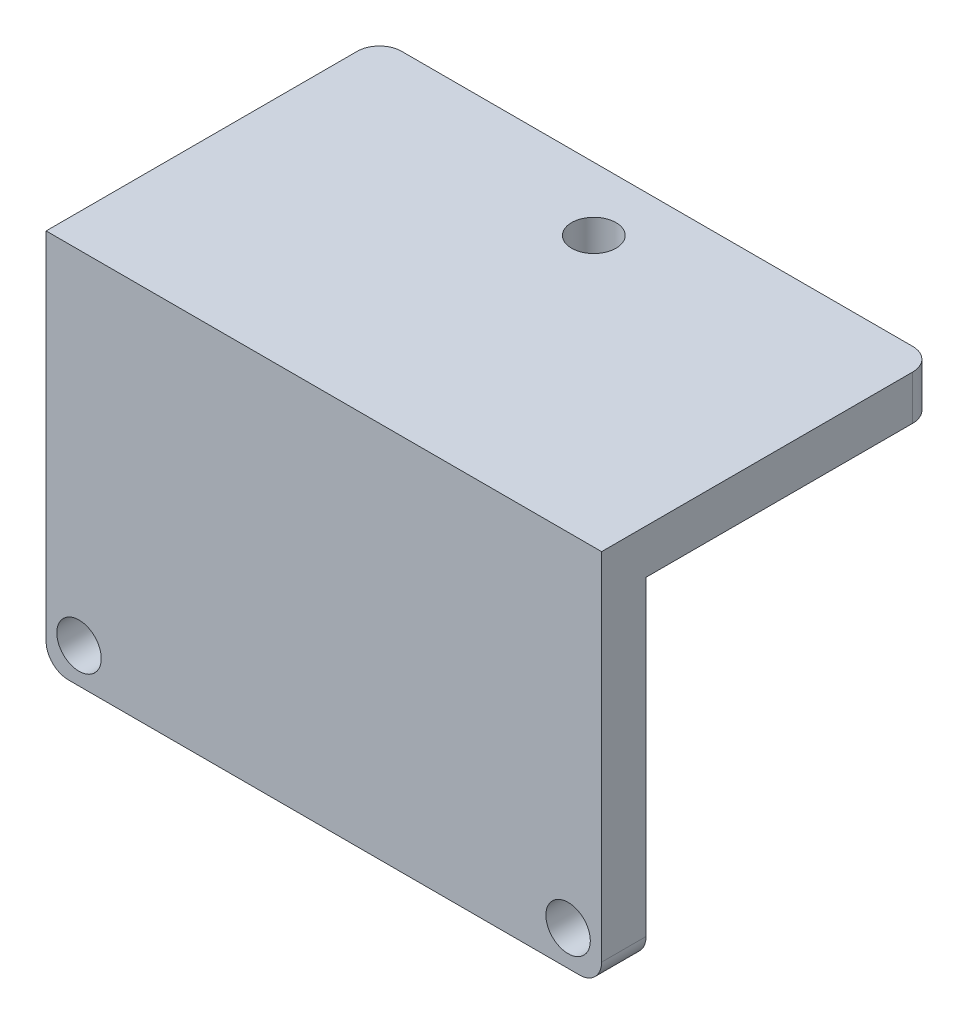
SolidWorks part; units mm, degrees
ref_plane "Front Plane" through (0, 0, 0) normal (0, 0, 1) x (1, 0, 0)
ref_plane "Top Plane" through (0, 0, 0) normal (0, 1, 0) x (1, 0, 0)
ref_plane "Right Plane" through (0, 0, 0) normal (1, 0, 0) x (0, 0, -1)
sketch "Sketch1" plane through (0, 0, 0) normal (0, 0, 1) x (1, 0, 0)
  line L1 (0, 0) -> (-25, 0)
  line L2 (0, 0) -> (0, -15)
  line L3 (0, -15) -> (-25, -15)
  line L4 (-25, 0) -> (-25, -15)
  circle A0 centre (-23.5193, -13.4231) radius 1
  circle A1 centre (-1.5082, -13.4231) radius 1
  dimension "D1" = 25
  dimension "D2" = 15
extrude "Boss-Extrude1" add sketch "Sketch1" along normal blind 2
fillet "Fillet5" radius 1 2 edges at (-25, -15, 1) (0, -15, 1)
sketch "Sketch2" plane through (0, 0, 0) normal (0, 1, 0) x (1, 0, 0)
  line L0 (-25, -2) -> (0, -2)
  line L1 (0, -2) -> (0, 13)
  line L2 (0, 13) -> (-25, 13)
  line L3 (-25, 13) -> (-25, -2)
extrude "Boss-Extrude2" add sketch "Sketch2" along normal blind 2
fillet "Fillet6" radius 1 1 edges at (-25, 1, -13)
fillet "Fillet7" radius 1 1 edges at (0, 1, -13)
sketch "Sketch3" plane through (0, 2, 0) normal (0, 1, 0) x (1, 0, 0)
  circle A0 centre (-12.5, 10.1482) radius 1
extrude "Cut-Extrude1" cut sketch "Sketch3" against normal blind 32
